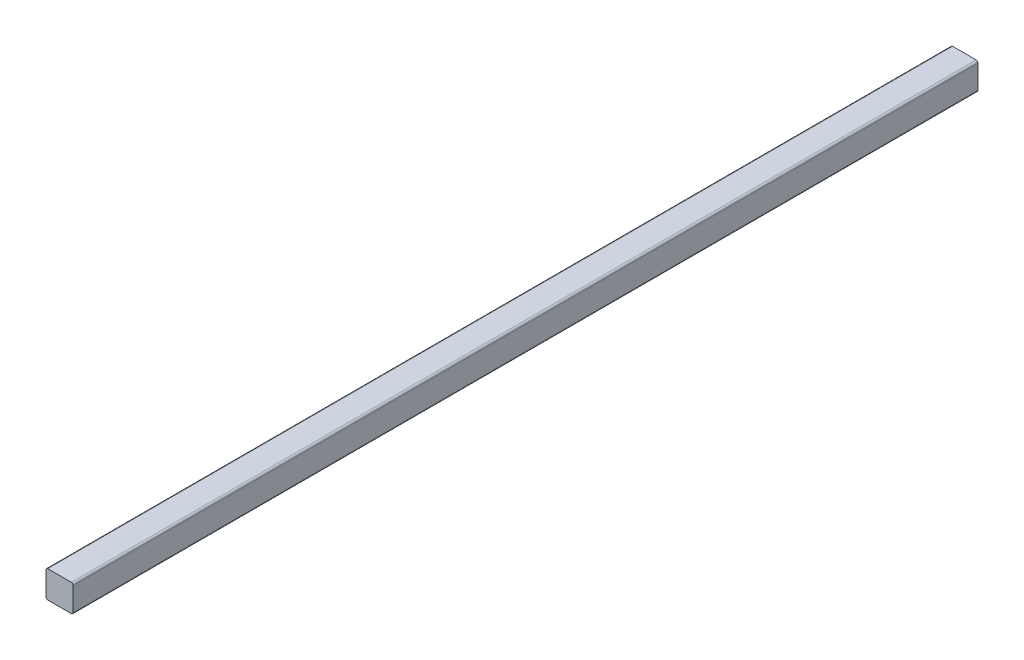
SolidWorks part; units mm, degrees
ref_plane "Front Plane" through (0, 0, 0) normal (0, 0, 1) x (1, 0, 0)
ref_plane "Top Plane" through (0, 0, 0) normal (0, 1, 0) x (1, 0, 0)
ref_plane "Right Plane" through (0, 0, 0) normal (1, 0, 0) x (0, 0, -1)
sketch "Sketch1" plane through (0, 0, 0) normal (0, 0, 1) x (1, 0, 0)
  line L0 (2, 0) -> (28, 0)
  line L1 (30, 2) -> (30, 28)
  line L2 (28, 30) -> (2, 30)
  line L3 (0, 28) -> (0, 2)
  arc A0 (2, 0) -> (0, 2) centre (2, 2) cw
  arc A1 (30, 2) -> (28, 0) centre (28, 2) cw
  arc A2 (28, 30) -> (30, 28) centre (28, 28) cw
  arc A3 (0, 28) -> (2, 30) centre (2, 28) cw
  point P7 (0, 0)
  dimension "D1" = 2
  dimension "D2" = 2
  dimension "D3" = 2
  dimension "D4" = 2
sketch "Sketch3" plane through (0, 0, 0) normal (0, 0, 1) x (1, 0, 0)
  line L0 (2, 0) -> (28, 0)
  line L1 (30, 2) -> (30, 28)
  line L2 (28, 30) -> (2, 30)
  line L3 (0, 28) -> (0, 2)
  arc A0 (2, 0) -> (0, 2) centre (2, 2) cw
  arc A1 (30, 2) -> (28, 0) centre (28, 2) cw
  arc A2 (28, 30) -> (30, 28) centre (28, 28) cw
  arc A3 (0, 28) -> (2, 30) centre (2, 28) cw
  dimension "D1" = 2
extrude "Boss-Extrude1" add sketch "Sketch3" along normal blind 1000
